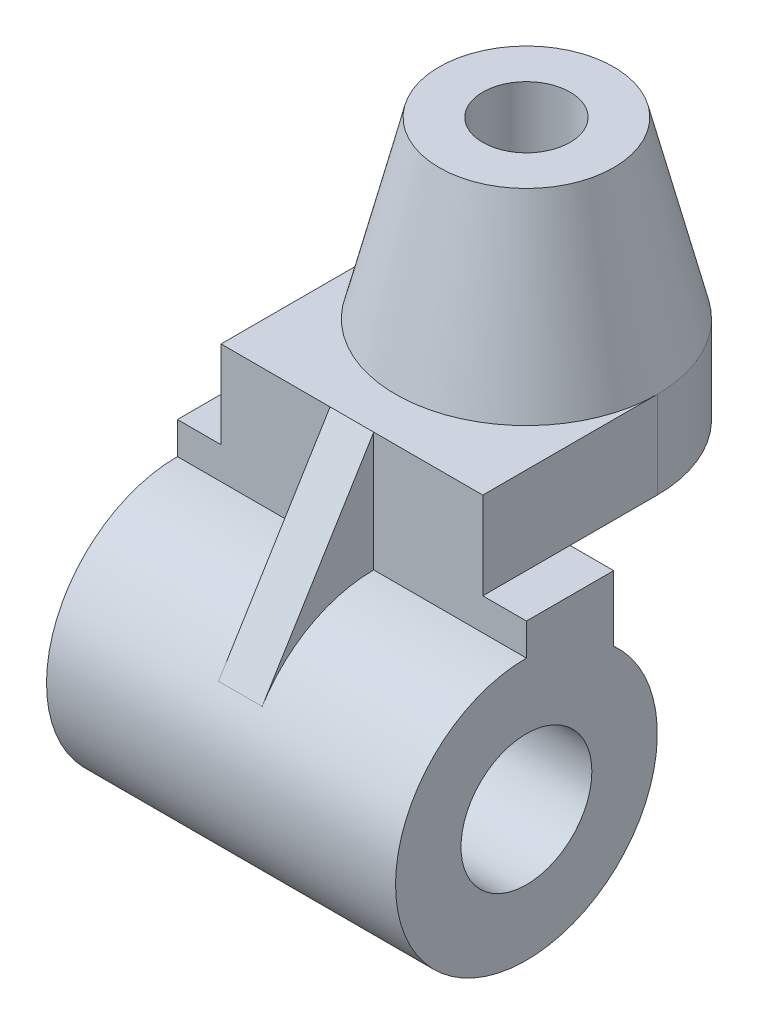
SolidWorks part; units mm, degrees
ref_plane "Front" through (0, 0, 0) normal (0, 0, 1) x (1, 0, 0)
ref_plane "Top" through (0, 0, 0) normal (0, 1, 0) x (1, 0, 0)
ref_plane "Right" through (0, 0, 0) normal (1, 0, 0) x (0, 0, -1)
sketch "Sketch1" plane through (0, 0, 0) normal (0, 1, 0) x (1, 0, 0)
  circle A0 centre (0, 0) radius 20
  dimension "D1" = 40
ref_plane "Plane1" through (0, -40, 0) normal (0, 1, 0) x (1, 0, 0)
sketch "Sketch2" plane through (0, -40, 0) normal (0, 1, 0) x (1, 0, 0)
  circle A0 centre (0, 0) radius 30
  dimension "D1" = 60
loft "Loft1" add profiles "Sketch1", "Sketch2"
sketch "Sketch3" plane through (0, 0, 0) normal (0, 1, 0) x (1, 0, 0)
  circle A0 centre (0, 0) radius 10
  dimension "D1" = 20
extrude "Cut-Extrude1" cut sketch "Sketch3" against normal through all
ref_plane "Plane2" through (0, -40, 0) normal (0, 1, 0) x (1, 0, 0)
sketch "Sketch6" plane through (0, -40, 0) normal (0, 1, 0) x (1, 0, 0)
  line L0 (-30, 0) -> (-30, -40)
  line L1 (-30, -40) -> (30, -40)
  line L2 (30, -40) -> (30, 0)
  circle A0 centre (0, 0) radius 30 construction
  arc A1 (-30, 0) -> (30, 0) centre (0, 0) cw
  dimension "D1" = 40
  dimension "D2" = 60
extrude "Boss-Extrude1" add sketch "Sketch6" against normal blind 20 contours A1 L0 L1 L2
sketch "Sketch7" plane through (30, 0, 0) normal (1, 0, 0) x (0, 0, -1)
  line L0 (-20, -60) -> (-20, -75)
  line L1 (-40, -60) -> (0, -60) construction
  line L2 (-20, -60) -> (-40, -60)
  line L3 (-40, -60) -> (-40, -67.3607)
  circle A0 centre (-40, -97.3607) radius 30
  circle A1 centre (-40, -97.3607) radius 15
  line M4 (-40, -60) -> (0, -60)
  dimension "D2" = 60
  dimension "D3" = 30
  dimension "D1" = 15
extrude "Boss-Extrude2" add sketch "Sketch7" against normal blind 70 and the other way blind 10 contours A0 A1 | A0 L0 L3 M4
ref_plane "Plane3" through (0, 0, 40) normal (0, 0, 1) x (1, 0, 0)
ref_plane "Plane5" through (0, 0, 0) normal (1, 0, 0) x (0, 0, -1)
sketch "Sketch11" plane through (0, 0, 0) normal (1, 0, 0) x (0, 0, -1)
  line L0 (-40, -40) -> (-65.5699, -81.6705)
  arc A0 (-40, -67.3607) -> (-20, -75) centre (-40, -97.3607) ccw construction
rib "Rib1" sketch "Sketch11" sketch "Sketch11" thickness 10 extrusion direction parallel to sketch draft on no parameters "D1"=10
